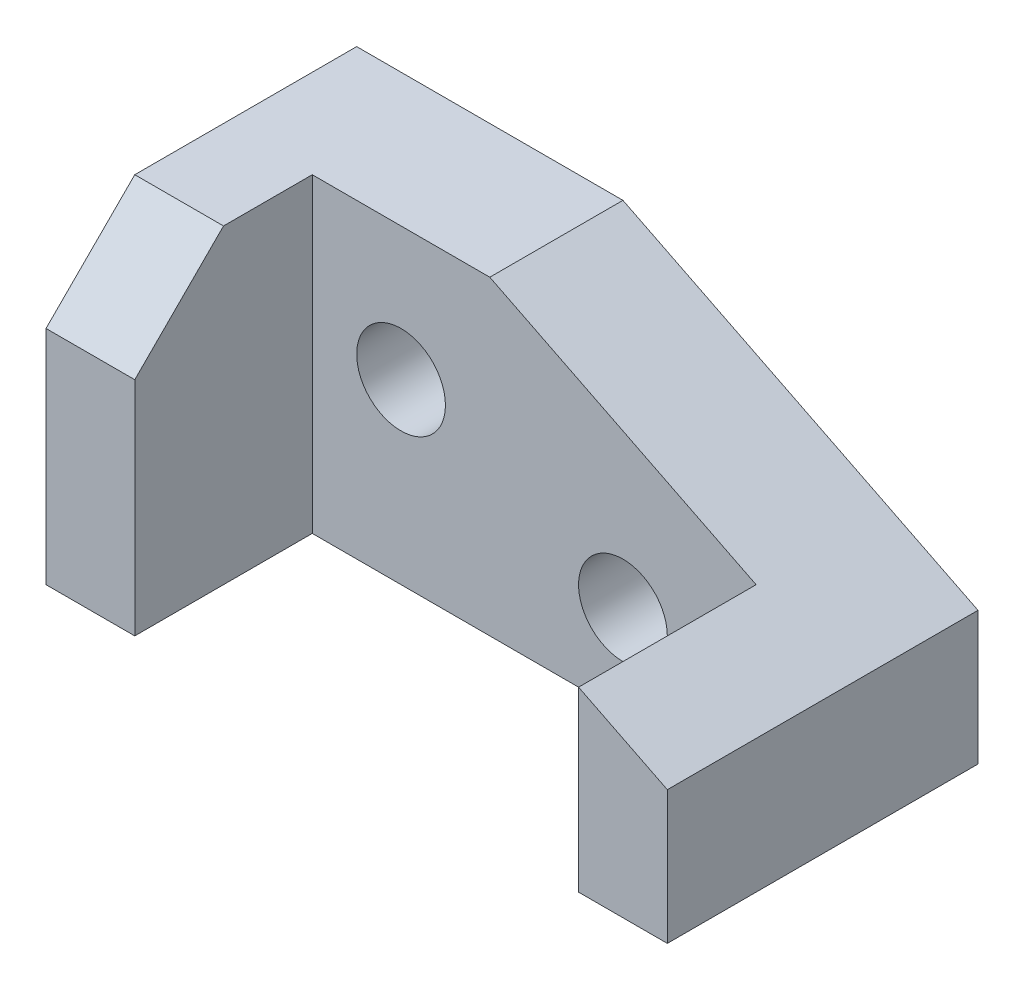
SolidWorks part; units mm, degrees
ref_plane "Front Plane" through (0, 0, 0) normal (0, 0, 1) x (1, 0, 0)
ref_plane "Top Plane" through (0, 0, 0) normal (0, 1, 0) x (1, 0, 0)
ref_plane "Right Plane" through (0, 0, 0) normal (1, 0, 0) x (0, 0, -1)
sketch "Sketch1" plane through (0, 0, 0) normal (0, 1, 0) x (1, 0, 0)
  line L1 (0, 0) -> (70, 0)
  line L2 (0, 0) -> (0, 35)
  line L3 (0, 35) -> (70, 35)
  line L4 (70, 0) -> (70, 35)
  dimension "D1" = 70
  dimension "D2" = 35
extrude "Boss-Extrude1" add sketch "Sketch1" along normal blind 35
sketch "Sketch2" plane through (0, 35, 0) normal (0, 1, 0) x (1, 0, 0)
  line L0 (0, 0) -> (10, 0) construction
  line L1 (0, 0) -> (70, 0) construction
  line L3 (10, 0) -> (60, 0)
  line L4 (10, 0) -> (10, 20)
  line L5 (10, 20) -> (60, 20)
  line L6 (60, 0) -> (60, 20)
  dimension "D1" = 20
  dimension "D2" = 50
extrude "Cut-Extrude1" cut sketch "Sketch2" against normal through all
sketch "Sketch3" plane through (0, 0, -35) normal (0, 0, -1) x (-1, 0, 0)
  line L0 (-70, 35) -> (-70, 15)
  line L1 (-70, 35) -> (-70, 0) construction
  line L2 (-70, 15) -> (-30, 35)
  line L3 (-70, 35) -> (0, 35) construction
  line L4 (-30, 35) -> (-70, 35)
  dimension "D1" = 20
  dimension "D2" = 40
extrude "Cut-Extrude2" cut sketch "Sketch3" against normal through all
sketch "Sketch4" plane through (0, 0, 0) normal (-1, 0, 0) x (0, 0, 1)
  line L0 (0, 35) -> (-10, 35)
  line L1 (-35, 35) -> (0, 35) construction
  line L2 (-10, 35) -> (0, 25)
  line L3 (0, 35) -> (0, 0) construction
  line L4 (0, 25) -> (0, 35)
  dimension "D1" = 10
  dimension "D2" = 10
extrude "Cut-Extrude3" cut sketch "Sketch4" against normal blind 35
sketch "Sketch5" plane through (0, 0, -20) normal (0, 0, 1) x (1, 0, 0)
  line L0 (30, 35) -> (20, 35) construction
  line L1 (30, 35) -> (10, 35) construction
  line L2 (20, 35) -> (20, 20) construction
  circle A0 centre (20, 20) radius 5
  dimension "D2" = 10
  dimension "D1" = 15
extrude "Cut-Extrude4" cut sketch "Sketch5" against normal blind 35
sketch "Sketch6" plane through (0, 0, -20) normal (0, 0, 1) x (1, 0, 0)
  line L0 (10, 0) -> (45, 0) construction
  line L1 (60, 0) -> (10, 0) construction
  line L2 (45, 0) -> (45, 10) construction
  circle A0 centre (45, 10) radius 5
  dimension "D1" = 10
  dimension "D2" = 35
extrude "Cut-Extrude5" cut sketch "Sketch6" against normal blind 35
